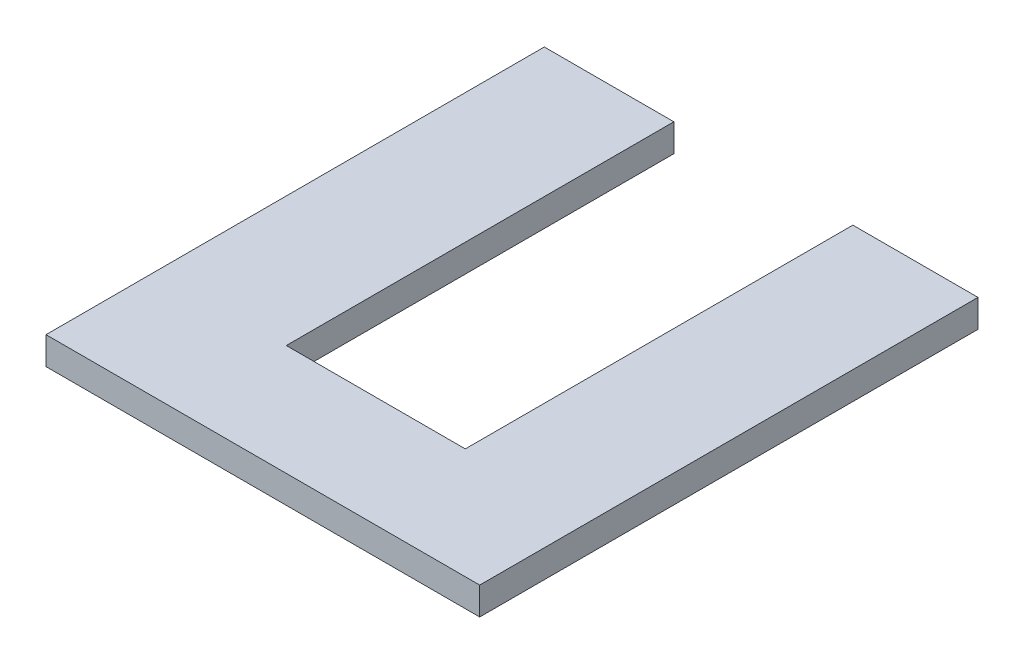
SolidWorks part; units mm, degrees
ref_plane "Plano frontal" through (0, 0, 0) normal (0, 0, 1) x (1, 0, 0)
ref_plane "Plano superior" through (0, 0, 0) normal (0, 1, 0) x (1, 0, 0)
ref_plane "Plano direito" through (0, 0, 0) normal (1, 0, 0) x (0, 0, -1)
sketch "Esboço1" plane through (0, 0, 0) normal (0, 0, 1) x (1, 0, 0)
  line L1 (0, 0) -> (2350, 0)
  line L2 (0, 0) -> (0, 150)
  line L3 (0, 150) -> (2350, 150)
  line L4 (2350, 0) -> (2350, 150)
  dimension "D1" = 150
  dimension "D2" = 2350
extrude "Ressalto-extrusão1" add sketch "Esboço1" along normal blind 2700
sketch "Esboço2" plane through (0, 150, 0) normal (0, 1, 0) x (1, 0, 0)
  line L1 (702, 0) -> (1672, 0)
  line L2 (702, 0) -> (702, -2100)
  line L3 (702, -2100) -> (1672, -2100)
  line L4 (1672, 0) -> (1672, -2100)
  line L6 (2350, 0) -> (0, 0) construction
  line L7 (2350, -2700) -> (2350, 0) construction
  dimension "D1" = 970
  dimension "D2" = 678
  dimension "D3" = 2100
  dimension "D4" = 0
extrude "Corte-extrusão1" cut sketch "Esboço2" against normal through all
